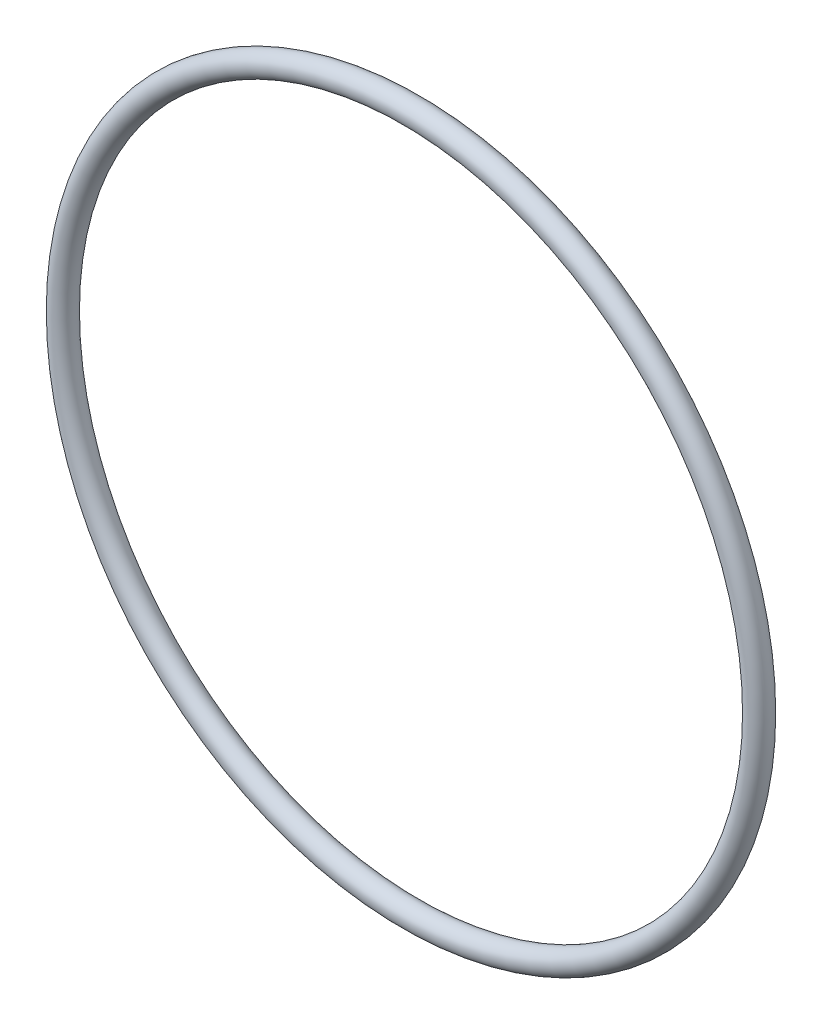
SolidWorks part; units mm, degrees
ref_plane "Front" through (0, 0, 0) normal (0, 0, 1) x (1, 0, 0)
ref_plane "Top" through (0, 0, 0) normal (0, 1, 0) x (1, 0, 0)
ref_plane "Right" through (0, 0, 0) normal (1, 0, 0) x (0, 0, -1)
sketch "Sketch1" plane through (0, 0, 0) normal (1, 0, 0) x (0, -1, 0)
  line L0 (0, -1.7653) -> (0, 1.7653) construction
  line L2 (-59.5401, 0) -> (59.5401, 0) construction
  line L3 (-50.5968, 0) -> (50.5968, 0) construction
  circle A0 centre (52.3621, 0) radius 1.7653
  point P9 (50.5968, 0)
  point P10 (54.1274, 0)
  point P13 (52.3621, 1.7653)
  point P14 (52.3621, -1.7653)
  dimension "Width" = 3.5306
  dimension "ID" = 101.1936
revolve "Revolve1" add sketch "Sketch1" angle 360 about L0
